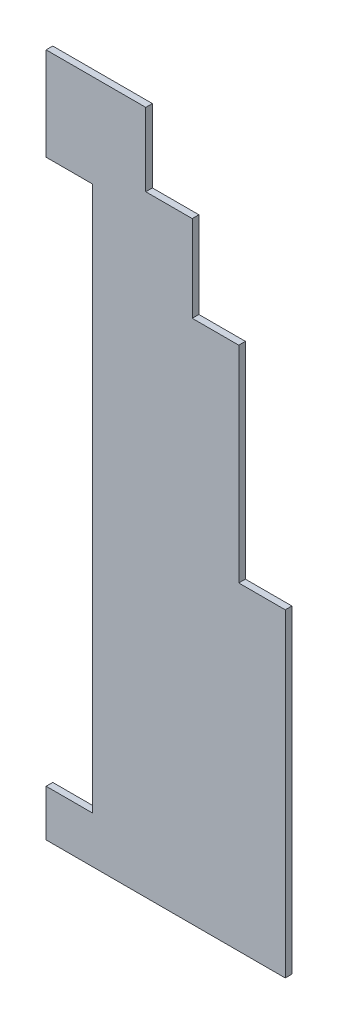
SolidWorks part; units mm, degrees
ref_plane "Plano frontal" through (0, 0, 0) normal (0, 0, 1) x (1, 0, 0)
ref_plane "Plano superior" through (0, 0, 0) normal (0, 1, 0) x (1, 0, 0)
ref_plane "Plano direito" through (0, 0, 0) normal (1, 0, 0) x (0, 0, -1)
sketch "Esboço1" plane through (0, 0, 0) normal (0, 0, 1) x (1, 0, 0)
  line L0 (0, 103) -> (15, 103)
  line L1 (15, 103) -> (15, 92)
  line L2 (36, 0) -> (0, 0)
  line L3 (15, 92) -> (22, 92)
  line L4 (22, 92) -> (22, 79)
  line L5 (22, 79) -> (29, 79)
  line L6 (29, 79) -> (29, 48)
  line L7 (0, 103) -> (0, 89)
  line L8 (0, 89) -> (7, 89)
  line L9 (7, 89) -> (7, 7)
  line L10 (7, 7) -> (0, 7)
  line L11 (0, 7) -> (0, 0)
  line L12 (29, 48) -> (36, 48)
  line L13 (36, 48) -> (36, 0)
  dimension "D1" = 103
  dimension "D2" = 7
  dimension "D3" = 82
  dimension "D4" = 7
  dimension "D5" = 92
  dimension "D6" = 79
  dimension "D7" = 48
  dimension "D8" = 7
  dimension "D9" = 15
extrude "Ressalto-extrusão1" add sketch "Esboço1" along normal blind 1
